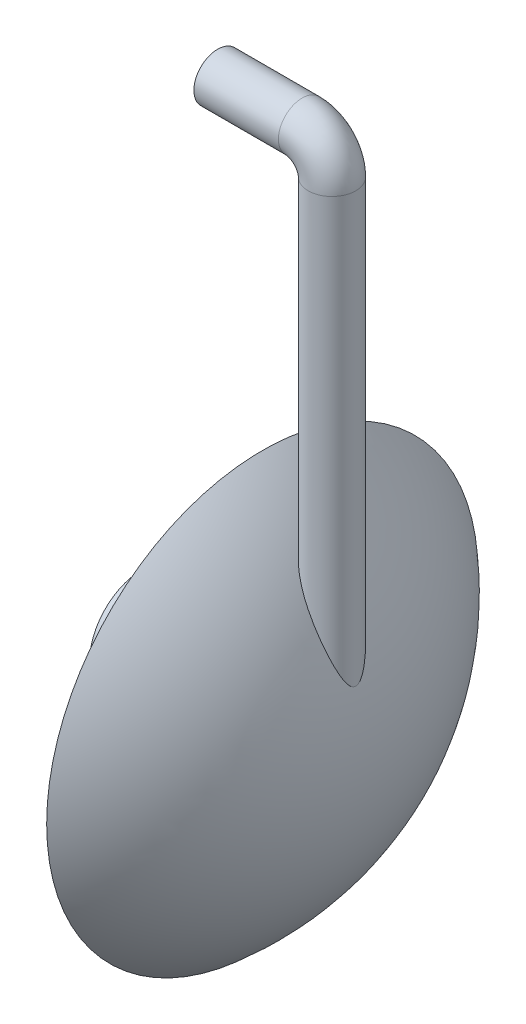
SolidWorks part; units mm, degrees
ref_plane "Front Plane" through (0, 0, 0) normal (0, 0, 1) x (1, 0, 0)
ref_plane "Top Plane" through (0, 0, 0) normal (0, 1, 0) x (1, 0, 0)
ref_plane "Right Plane" through (0, 0, 0) normal (1, 0, 0) x (0, 0, -1)
sketch "Sketch2" plane through (0, 0, 0) normal (0, 1, 0) x (1, 0, 0)
  line L0 (0, 0) -> (0, -216.9534)
  line L1 (100, 0) -> (0, 0)
  arc A1 (0, -216.9534) -> (100, 0) centre (-185.3438, 0) ccw
  dimension "D1" = 216.9534
  dimension "D2" = 100
revolve "Revolve1" add sketch "Sketch2" angle 360 about L1
sketch "Sketch4" plane through (0, 0, 0) normal (0, 0, 1) x (1, 0, 0)
  line L0 (0, 0) -> (0, 140) construction
  line L1 (0, 140) -> (207.1523, 140) construction
  line L2 (75, 140) -> (75, 490)
  line L3 (40, 525) -> (-45, 525)
  arc A0 (75, 490) -> (40, 525) centre (40, 490) ccw
  dimension "D1" = 35
  dimension "D6" = 140
  dimension "D2" = 85
  dimension "D4" = 385
  dimension "D3" = 75
ref_plane "Plane1" through (0, 140, 0) normal (0, 1, 0) x (1, 0, 0)
shell "Shell3" thickness 59.7668
sketch "Sketch6" plane through (0, 0, 0) normal (-1, 0, 0) x (0, 0, 1)
  circle A0 centre (0, 0) radius 53.7901
  dimension "D1" = 107.5802
extrude "Boss-Extrude2" add sketch "Sketch6" along normal blind 120 and the other way up to next
sketch "Sketch5" plane through (0, 140, 0) normal (0, 1, 0) x (1, 0, 0)
  line L2 (0, 216.9534) -> (0, -216.9534) construction
  line L3 (0, 0) -> (207.1523, 0) construction
  circle A0 centre (70, 0) radius 23.9067
  dimension "D1" = 47.8134
  dimension "D2" = 70
sweep "Sweep2" add profiles "Sketch5" path "Sketch4"
sketch "Sketch7" plane through (0, 140, 0) normal (0, -1, 0) x (1, 0, 0)
  arc A2 (62.2636, -22.6203) -> (62.2636, 22.6203) centre (70, 0) ccw
  arc A3 (62.2636, -22.6203) -> (62.2636, 22.6203) centre (-185.3438, 0) ccw
  arc A4 (62.2636, -22.6203) -> (62.2636, 22.6203) centre (70, 0) ccw
  arc A5 (62.2636, -22.6203) -> (62.2636, 22.6203) centre (-185.3438, 0) ccw
  dimension "D1" = 0
extrude "Boss-Extrude3" add sketch "Sketch7" along normal up to next
equation "\"COVER_RADIUS\" = 181.5 * 205 / 171.5"
equation "\"D1@Sketch2\"=\"COVER_RADIUS\""
equation "\"D1@Shell3\"=\"COVER_RADIUS\"*500/1815"
equation "\"D2@Sketch5\"=\"COVER_RADIUS\"*300/1815"
equation "\"D1@Sketch5\" = \"COVER_RADIUS\" * 400 / 1815"
equation "\"D1@Sketch6\" = \"COVER_RADIUS\" * 900 / 1815"
equation "\"D6@Sketch4\"=\"COVER_RADIUS\"*1350/1815"
